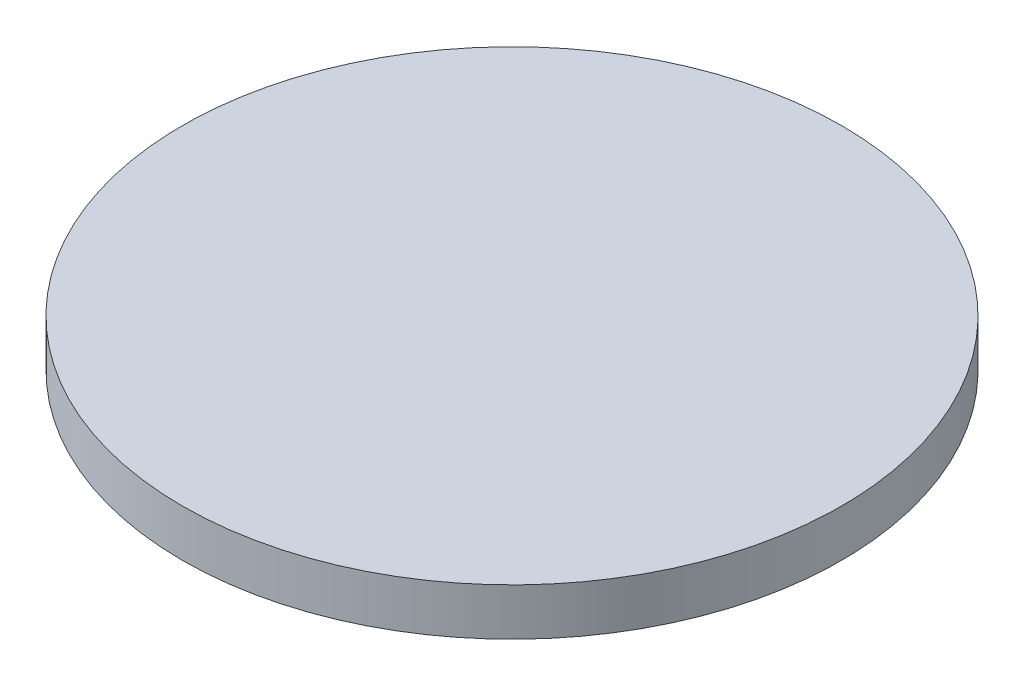
SolidWorks part; units mm, degrees
material "Thornel Mat VMA"
ref_plane "Front Plane" through (0, 0, 0) normal (0, 0, 1) x (1, 0, 0)
ref_plane "Top Plane" through (0, 0, 0) normal (0, 1, 0) x (1, 0, 0)
ref_plane "Right Plane" through (0, 0, 0) normal (1, 0, 0) x (0, 0, -1)
sketch "Sketch1" plane through (0, 0, 0) normal (0, 1, 0) x (1, 0, 0)
  circle A0 centre (0, 0) radius 22.225
  dimension "D1" = 44.45
extrude "Boss-Extrude1" add sketch "Sketch1" along normal blind 3.175
